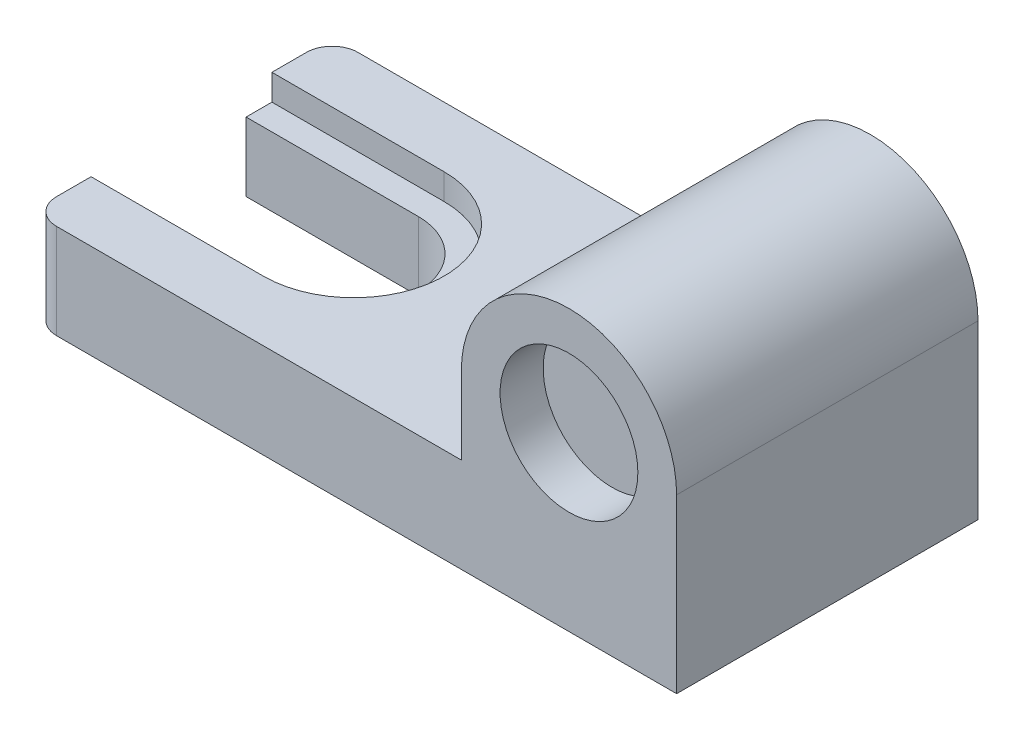
SolidWorks part; units mm, degrees
ref_plane "Ön Düzlem" through (0, 0, 0) normal (0, 0, 1) x (1, 0, 0)
ref_plane "Üst Düzlem" through (0, 0, 0) normal (0, 1, 0) x (1, 0, 0)
ref_plane "Sağ Düzlem" through (0, 0, 0) normal (1, 0, 0) x (0, 0, -1)
sketch "Çizim1" plane through (0, 0, 0) normal (0, 0, 1) x (1, 0, 0)
  line L1 (0, 0) -> (75, 0)
  line L2 (0, 0) -> (0, 36)
  line L3 (0, 36) -> (75, 36)
  line L4 (75, 0) -> (75, 36)
  dimension "D1" = 75
  dimension "D2" = 36
extrude "Yükseklik-Ekstrüzyon1" add sketch "Çizim1" along normal blind 35
sketch "Çizim2" plane through (0, 0, 35) normal (0, 0, 1) x (1, 0, 0)
  line L2 (0, 36) -> (50, 36)
  line L4 (0, 36) -> (0, 11)
  line L5 (0, 11) -> (50, 11)
  line L6 (50, 36) -> (50, 11)
  line L8 (75, 36) -> (0, 36) construction
  dimension "D1" = 50
  dimension "D2" = 25
extrude "Kes-Ekstrüzyon1" cut sketch "Çizim2" against normal through all
sketch "Çizim6" plane through (0, 0, 35) normal (0, 0, 1) x (1, 0, 0)
  line L0 (50, 20) -> (75, 20) construction
  line L1 (50, 11) -> (50, 36) construction
  line L2 (75, 0) -> (75, 36) construction
  line L3 (0, 0) -> (75, 0) construction
  circle A0 centre (62.5, 20) radius 8
  dimension "D2" = 16
  dimension "D1" = 20
extrude "Kes-Ekstrüzyon3" cut sketch "Çizim6" against normal blind 5
sketch "Çizim7" plane through (0, 11, 0) normal (0, 1, 0) x (1, 0, 0)
  line L0 (0, -7) -> (20, -7)
  line L1 (0, 0) -> (0, -35) construction
  line L2 (0, -28) -> (20, -28)
  line L4 (0, 0) -> (50, 0) construction
  line L5 (0, -35) -> (50, -35) construction
  line L6 (0, -7) -> (0, -10)
  line L7 (0, -10) -> (20, -10)
  line L8 (0, -28) -> (0, -25)
  line L9 (0, -25) -> (20, -25)
  arc A0 (20, -7) -> (20, -28) centre (20, -17.5) cw
  arc A1 (20, -25) -> (20, -10) centre (20, -17.5) ccw
  dimension "D5" = 7.5
  dimension "D1" = 20
  dimension "D2" = 7
  dimension "D3" = 7
  dimension "D4" = 3
extrude "Kes-Ekstrüzyon4" cut sketch "Çizim7" against normal blind 3
sketch "Çizim8" plane through (0, 11, 0) normal (0, 1, 0) x (1, 0, 0)
  line L1 (0, -10) -> (20, -10)
  line L2 (0, -10) -> (0, -25)
  line L3 (0, -25) -> (20, -25)
  arc A0 (20, -10) -> (20, -25) centre (20, -17.5) cw
extrude "Kes-Ekstrüzyon5" cut sketch "Çizim8" against normal through all and the other way through all
fillet "Radyus2" radius 3 1 edges at (0, 5.5, 0)
fillet "Radyus3" radius 3 1 edges at (0, 5.5, 35)
sketch "Çizim9" plane through (0, 0, 35) normal (0, 0, 1) x (1, 0, 0)
  line L0 (50, 20) -> (75, 20) construction
  line L1 (50, 11) -> (50, 36) construction
  line L2 (75, 0) -> (75, 36) construction
  line L3 (3, 0) -> (75, 0) construction
  line L6 (50, 20) -> (50, 36)
  line L7 (50, 36) -> (75, 36)
  line L8 (75, 36) -> (75, 20)
  arc A0 (75, 20) -> (50, 20) centre (62.5, 20) ccw
  dimension "D1" = 20
extrude "Kes-Ekstrüzyon7" cut sketch "Çizim9" against normal through all
